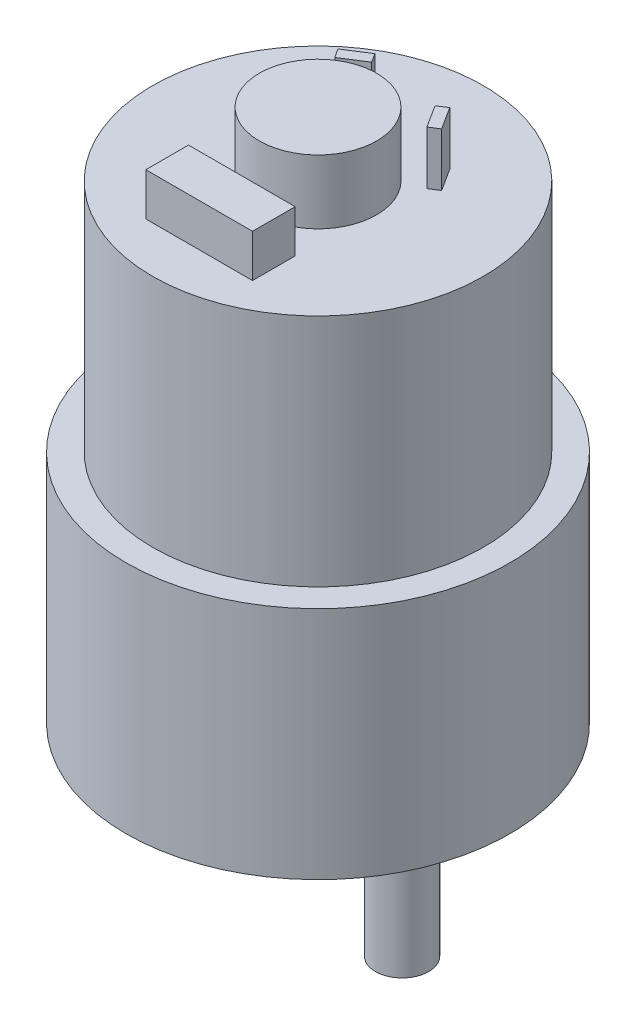
SolidWorks part; units mm, degrees
ref_plane "前视基准面" through (0, 0, 0) normal (0, 0, 1) x (1, 0, 0)
ref_plane "上视基准面" through (0, 0, 0) normal (0, 1, 0) x (1, 0, 0)
ref_plane "右视基准面" through (0, 0, 0) normal (1, 0, 0) x (0, 0, -1)
sketch "草图1" plane through (0, 0, 0) normal (0, 1, 0) x (1, 0, 0)
  circle A0 centre (0, 0) radius 18
extrude "凸台-拉伸1" add sketch "草图1" along normal blind 22
sketch "草图2" plane through (0, 22, 0) normal (0, 1, 0) x (1, 0, 0)
  circle A0 centre (0, 0) radius 15.5
extrude "凸台-拉伸2" add sketch "草图2" along normal blind 22
sketch "草图3" plane through (0, 0, 0) normal (0, -1, 0) x (1, 0, 0)
  circle A0 centre (7.9875, 0) radius 5
  point P2 (11.9451, -68.2571)
  point P3 (0, 0)
extrude "凸台-拉伸4" add sketch "草图3" along normal blind 3
sketch "草图4" plane through (0, -3, 0) normal (0, -1, 0) x (1, 0, 0)
  circle A0 centre (7.8847, 0) radius 2.5
  point P2 (0, 0)
  point P3 (0, 0)
  point P4 (0, 0)
  point P5 (6.5496, 0.8464)
  point P6 (7.8847, 0)
extrude "凸台-拉伸5" add sketch "草图4" along normal blind 12 contours A0
sketch "草图5" plane through (0, 44, 0) normal (0, 1, 0) x (1, 0, 0)
  circle A0 centre (0, 0) radius 5.5
extrude "凸台-拉伸6" add sketch "草图5" along normal blind 6
sketch "草图6" plane through (0, 44, 0) normal (0, 1, 0) x (1, 0, 0)
  line L0 (-4.7785, 6.6538) -> (-2.6664, 8.0019)
  line L2 (5.2234, 7.1296) -> (6.5685, 5.0223)
  point P4 (0, 0)
  point P6 (0, 0)
  point P7 (0, 0)
  point P8 (0, 0)
  point P9 (0, 0)
  point P10 (0, 0)
  point P11 (0, 0)
  point P12 (0, 0)
  point P13 (0, 0)
  point P14 (0, 0)
  point P15 (0, 0)
  point P16 (0, 0)
  point P17 (0, 0)
  point P18 (6.106, 11.5848)
extrude "拉伸-薄壁1" add sketch "草图6" along normal blind 5.0039 thin
sketch "草图7" plane through (0, 44, 0) normal (0, 1, 0) x (1, 0, 0)
  line L1 (-4.9856, -7.1553) -> (5.0144, -7.1553)
  line L2 (-4.9856, -7.1553) -> (-4.9856, -11.1553)
  line L3 (-4.9856, -11.1553) -> (5.0144, -11.1553)
  line L4 (5.0144, -7.1553) -> (5.0144, -11.1553)
  dimension "D1" = 10
  dimension "D2" = 4
extrude "凸台-拉伸7" add sketch "草图7" along normal blind 4
